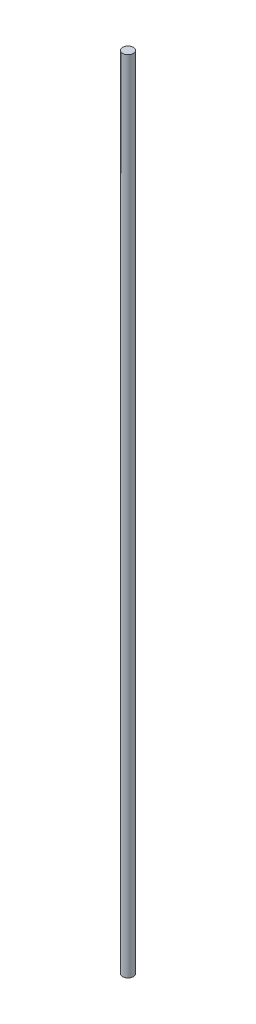
SolidWorks part; units mm, degrees
ref_plane "Front Plane" through (0, 0, 0) normal (0, 0, 1) x (1, 0, 0)
ref_plane "Top Plane" through (0, 0, 0) normal (0, 1, 0) x (1, 0, 0)
ref_plane "Right Plane" through (0, 0, 0) normal (1, 0, 0) x (0, 0, -1)
sketch "Sketch1" plane through (0, 0, 0) normal (0, 1, 0) x (1, 0, 0)
  circle A0 centre (0, 0) radius 1
  dimension "D1" = 2
extrude "Boss-Extrude2" add sketch "Sketch1" along normal blind 150 contours A0
